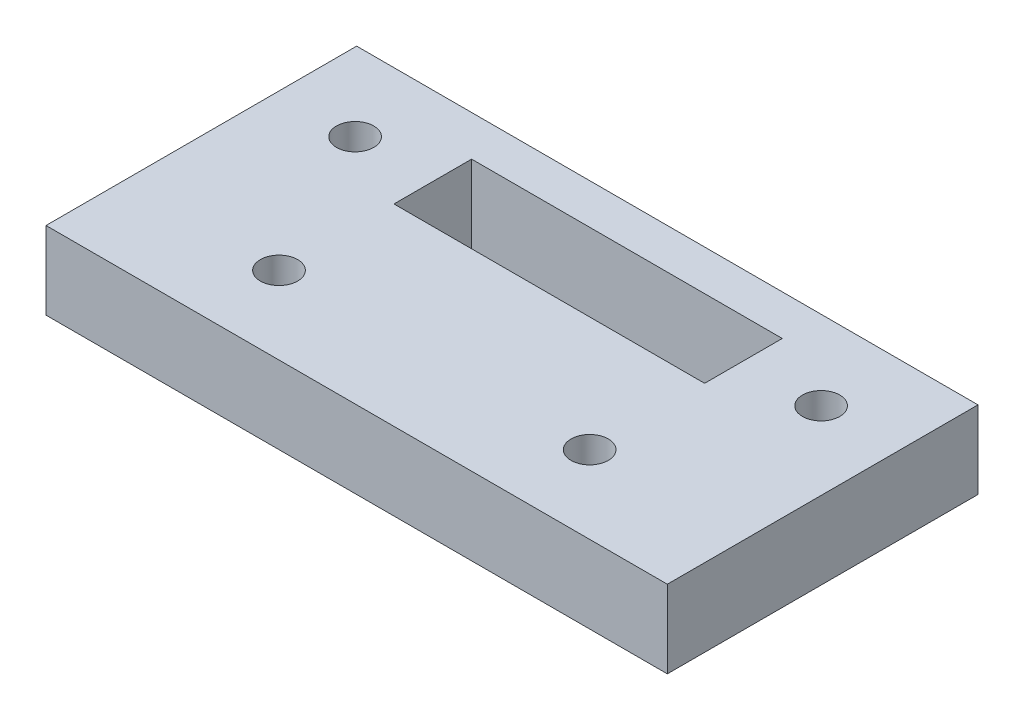
SolidWorks part; units mm, degrees
ref_plane "Front Plane" through (0, 0, 0) normal (0, 0, 1) x (1, 0, 0)
ref_plane "Top Plane" through (0, 0, 0) normal (0, 1, 0) x (1, 0, 0)
ref_plane "Right Plane" through (0, 0, 0) normal (1, 0, 0) x (0, 0, -1)
sketch "Sketch1" plane through (0, 0, 0) normal (0, 1, 0) x (1, 0, 0)
  line L0 (25.4, 0) -> (25.4, -25.4) construction
  line L1 (0, 0) -> (50.8, 0)
  line L2 (0, 0) -> (0, -25.4)
  line L3 (0, -25.4) -> (50.8, -25.4)
  line L4 (50.8, 0) -> (50.8, -25.4)
  line L5 (12.7, -3.302) -> (38.1, -3.302)
  line L6 (12.7, -3.302) -> (12.7, -9.652)
  line L7 (12.7, -9.652) -> (38.1, -9.652)
  line L8 (38.1, -3.302) -> (38.1, -9.652)
  circle A0 centre (6.35, -6.477) radius 1.524
  circle A1 centre (44.45, -6.477) radius 1.524
  circle A2 centre (12.7, -19.05) radius 1.524
  circle A3 centre (38.1, -19.05) radius 1.524
  point P11 (12.7, -6.477)
  dimension "D6" = 3.048
  dimension "D7" = 6.35
  dimension "D10" = 3.048
  dimension "D11" = 12.7
  dimension "D1" = 50.8
  dimension "D2" = 25.4
  dimension "D3" = 25.4
  dimension "D4" = 3.302
  dimension "D5" = 12.7
  dimension "D8" = 6.35
  dimension "D9" = 3.175
  dimension "D12" = 6.35
extrude "Boss-Extrude1" add sketch "Sketch1" along normal blind 6.35
